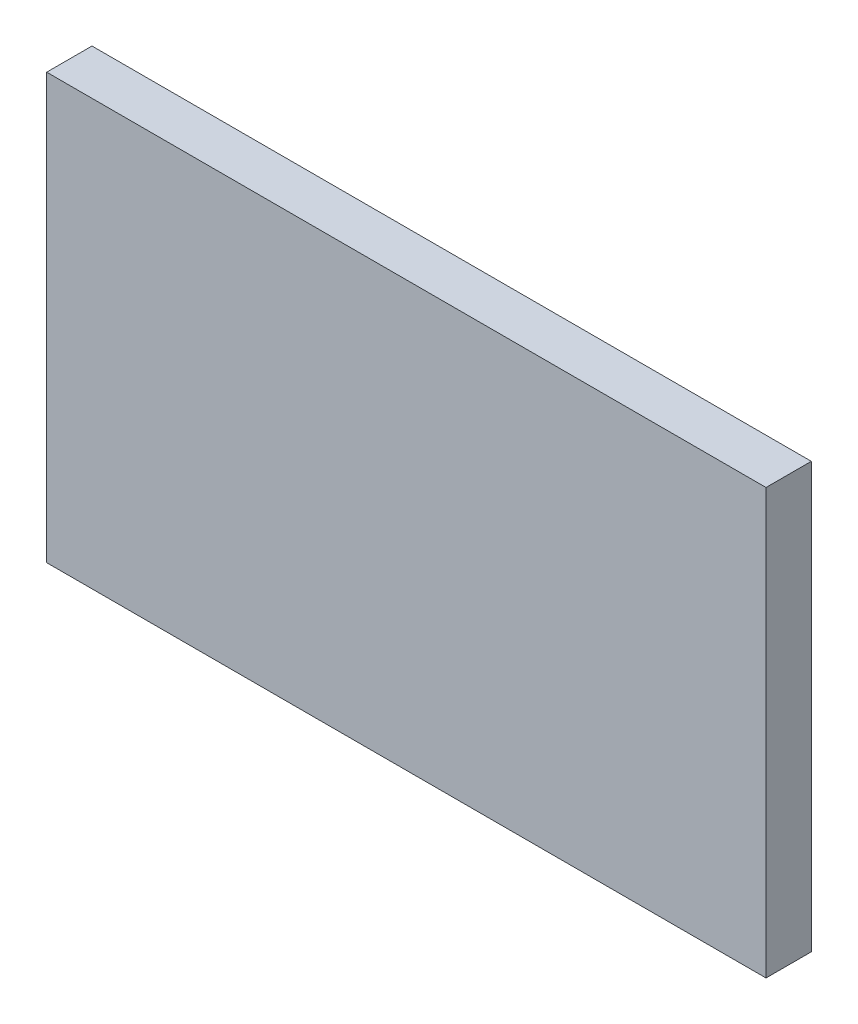
SolidWorks part; units mm, degrees
ref_plane "Alzado" through (0, 0, 0) normal (0, 0, 1) x (1, 0, 0)
ref_plane "Planta" through (0, 0, 0) normal (0, 1, 0) x (1, 0, 0)
ref_plane "Vista lateral" through (0, 0, 0) normal (1, 0, 0) x (0, 0, -1)
sketch "Croquis1" plane through (0, 0, 0) normal (0, 0, 1) x (1, 0, 0)
  line L5 (0, 0) -> (101.6, 0)
  line L6 (0, 0) -> (0, 60)
  line L7 (0, 60) -> (101.6, 60)
  line L8 (101.6, 0) -> (101.6, 60)
extrude "Saliente-Extruir1" add sketch "Croquis1" along normal blind 6.4
